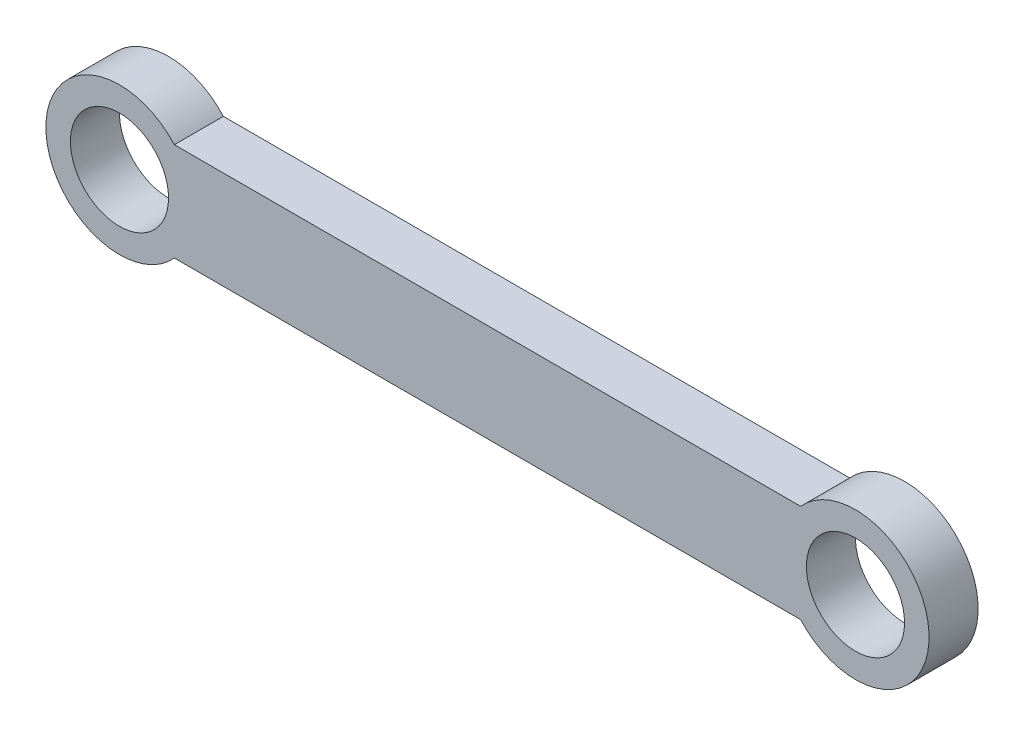
SolidWorks part; units mm, degrees
material "可锻铸铁"
ref_plane "前视基准面" through (0, 0, 0) normal (0, 0, 1) x (1, 0, 0)
ref_plane "上视基准面" through (0, 0, 0) normal (0, 1, 0) x (1, 0, 0)
ref_plane "右视基准面" through (0, 0, 0) normal (1, 0, 0) x (0, 0, -1)
sketch "草图1" plane through (0, 0, 0) normal (0, 0, 1) x (1, 0, 0)
  line L1 (-12.7639, 2) -> (12.7639, 2)
  line L3 (-12.7639, -2) -> (12.7639, -2)
  arc A0 (12.7639, -2) -> (12.7639, 2) centre (15, 0) ccw
  arc A1 (-12.7639, 2) -> (-12.7639, -2) centre (-15, 0) ccw
  circle A2 centre (-15, 0) radius 2
  circle A3 centre (15, 0) radius 2
  point P0 (0, 0)
  dimension "D3" = 6
  dimension "D4" = 6
  dimension "D1" = 4
  dimension "D2" = 4
extrude "凸台-拉伸1" add sketch "草图1" along normal blind 2
